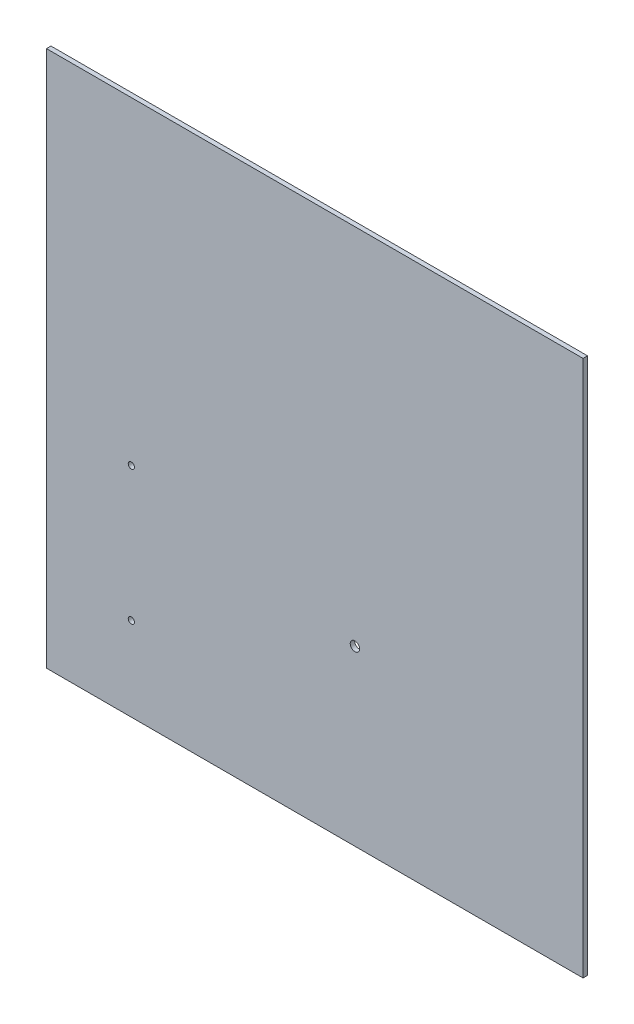
SolidWorks part; units mm, degrees
material "Maple"
ref_plane "Front Plane" through (0, 0, 0) normal (0, 0, 1) x (1, 0, 0)
ref_plane "Top Plane" through (0, 0, 0) normal (0, 1, 0) x (1, 0, 0)
ref_plane "Right Plane" through (0, 0, 0) normal (1, 0, 0) x (0, 0, -1)
sketch "Sketch1" plane through (0, 0, 0) normal (0, 0, 1) x (1, 0, 0)
  line L1 (0, 0) -> (304.8, 0)
  line L2 (0, 0) -> (0, 304.8)
  line L3 (0, 304.8) -> (304.8, 304.8)
  line L4 (304.8, 0) -> (304.8, 304.8)
  dimension "D1" = 304.8
  dimension "D2" = 304.8
extrude "Boss-Extrude1" add sketch "Sketch1" along normal blind 2.54
sketch "Sketch2" plane through (0, 0, 2.54) normal (0, 0, 1) x (1, 0, 0)
  circle A2 centre (48.205, 47.5897) radius 1.7526
  circle A3 centre (175.205, 98.3897) radius 2.667
  circle A4 centre (48.205, 123.7897) radius 1.7526
  dimension "D1" = 3.5052
  dimension "D2" = 5.334
  dimension "D6" = 3.5052
  dimension "D3" = 127
  dimension "D4" = 50.8
  dimension "D5" = 76.2
extrude "Cut-Extrude1" cut sketch "Sketch2" against normal through all both and the other way through all
